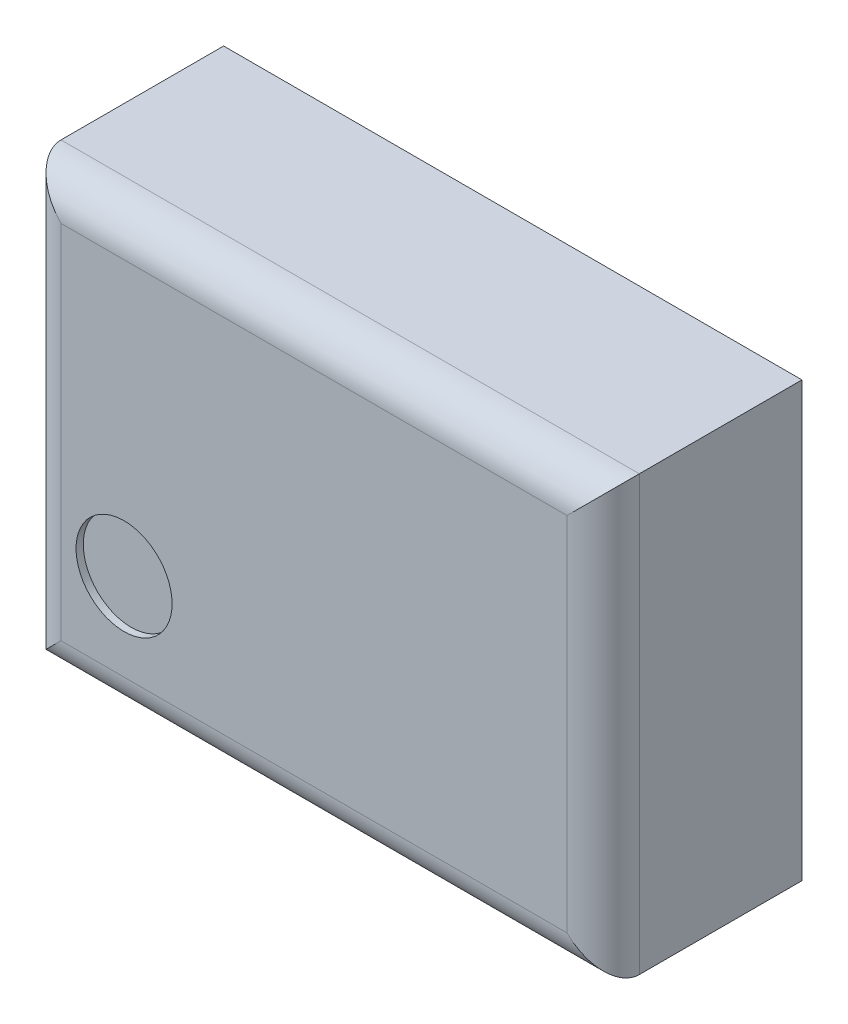
SolidWorks part; units mm, degrees
ref_plane "Front Plane" through (0, 0, 0) normal (0, 0, 1) x (1, 0, 0)
ref_plane "Top Plane" through (0, 0, 0) normal (0, 1, 0) x (1, 0, 0)
ref_plane "Right Plane" through (0, 0, 0) normal (1, 0, 0) x (0, 0, -1)
sketch "Sketch1" plane through (0, 0, 0) normal (0, 0, 1) x (1, 0, 0)
  line L1 (-0.8, -0.6) -> (0.8, -0.6)
  line L2 (-0.8, -0.6) -> (-0.8, 0.6)
  line L3 (-0.8, 0.6) -> (0.8, 0.6)
  line L4 (0.8, -0.6) -> (0.8, 0.6)
  line L5 (-0.8, -0.6) -> (0.8, 0.6) construction
  line L6 (-0.8, 0.6) -> (0.8, -0.6) construction
  point P0 (0, 0)
  dimension "D1" = 1.6
  dimension "D2" = 1.2
extrude "Boss-Extrude1" add sketch "Sketch1" along normal blind 0.55 from offset 0.05
sketch "Sketch2" plane through (0, 0, 0) normal (0, 0, 1) x (1, 0, 0)
  line L0 (-0.75, 0.15) -> (-0.25, 0.15)
  line L1 (-0.75, -0.55) -> (-0.25, -0.55)
  line L2 (-0.75, -0.55) -> (-0.75, -0.15)
  line L3 (-0.75, -0.15) -> (-0.25, -0.15)
  line L4 (-0.25, -0.55) -> (-0.25, -0.15)
  line L5 (-0.75, 0.15) -> (-0.75, 0.55)
  line L6 (-0.75, 0.55) -> (-0.25, 0.55)
  line L7 (-0.25, 0.15) -> (-0.25, 0.55)
  line L8 (0.25, 0.15) -> (0.75, 0.15)
  line L9 (0.25, 0.15) -> (0.25, 0.55)
  line L10 (0.25, 0.55) -> (0.75, 0.55)
  line L11 (0.75, 0.15) -> (0.75, 0.55)
  line L12 (0.25, -0.55) -> (0.75, -0.55)
  line L13 (0.25, -0.55) -> (0.25, -0.15)
  line L14 (0.25, -0.15) -> (0.75, -0.15)
  line L15 (0.75, -0.55) -> (0.75, -0.15)
  line L16 (-0.25, -0.35) -> (0.25, -0.35) construction
  line L17 (0.5, -0.15) -> (0.5, 0.15) construction
  line L18 (-0.2715, 0.3774) -> (0.2285, 0.3774) construction
  line L19 (-0.5, 0.15) -> (-0.5, -0.15) construction
  line L20 (-0.75, 0.35) -> (-0.8, 0.35) construction
  line L21 (-0.8, 0.6) -> (-0.8, -0.6) construction
  line L22 (0.75, 0.35) -> (0.8, 0.35) construction
  line L23 (-0.5, -0.55) -> (-0.5, -0.6) construction
  line L24 (-0.8, -0.6) -> (0.8, -0.6) construction
  line L25 (-0.5, 0.55) -> (-0.5, 0.6) construction
  line L26 (0.8, 0.6) -> (-0.8, 0.6) construction
  line L27 (0.8, -0.6) -> (0.8, 0.6) construction
  point P38 (0.8, 0.35)
  dimension "D1" = 0.5
  dimension "D2" = 0.4
  dimension "D3" = 0.4
  dimension "D4" = 0.4
  dimension "D5" = 0.4
  dimension "D6" = 0.5
  dimension "D7" = 0.5
  dimension "D8" = 0.5
  dimension "D9" = 0.3
  dimension "D10" = 0.5
extrude "Boss-Extrude2" add sketch "Sketch2" along normal up to next
fillet "Fillet1" radius 0.1 4 edges at (0, -0.6, 0.6) (-0.8, 0, 0.6) (0, 0.6, 0.6) (0.8, 0, 0.6)
sketch "Sketch3" plane through (0, 0, 0.6) normal (0, 0, 1) x (1, 0, 0)
  circle A0 centre (-0.5255, -0.258) radius 0.1328
extrude "Cut-Extrude1" cut sketch "Sketch3" against normal blind 0.02
